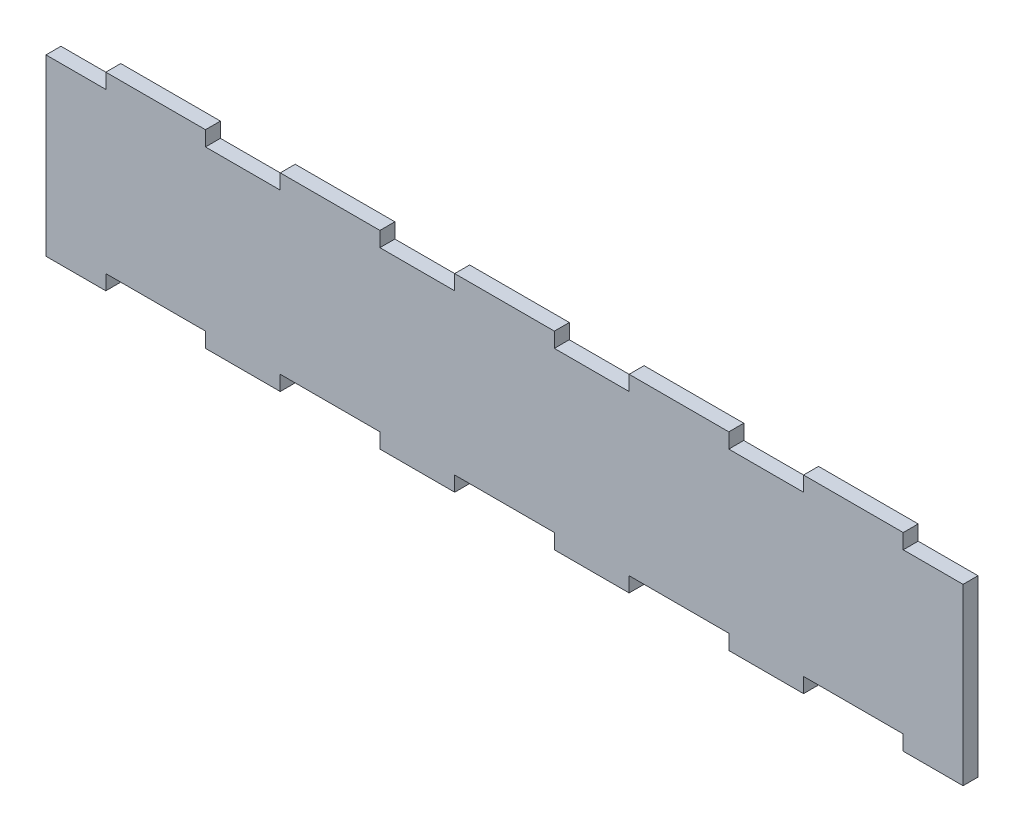
SolidWorks part; units mm, degrees
ref_plane "Front Plane" through (0, 0, 0) normal (0, 0, 1) x (1, 0, 0)
ref_plane "Top Plane" through (0, 0, 0) normal (0, 1, 0) x (1, 0, 0)
ref_plane "Right Plane" through (0, 0, 0) normal (1, 0, 0) x (0, 0, -1)
sketch "Sketch1" plane through (0, 0, 0) normal (0, 0, -1) x (1, 0, 0)
  line L0 (32, 0) -> (47, 0)
  line L1 (0, 0) -> (12, 0)
  line L2 (0, 0) -> (0, 35)
  line L3 (0, 35) -> (12, 35)
  line L4 (184, 0) -> (184, 35)
  line L5 (0, 0) -> (184, 35) construction
  line L6 (0, 35) -> (184, 0) construction
  line L7 (47, -3) -> (67, -3)
  line L8 (12, 0) -> (12, -3)
  line L9 (12, -3) -> (32, -3)
  line L10 (32, 0) -> (32, -3)
  line L11 (67, 0) -> (67, -3)
  line L12 (47, 0) -> (47, -3)
  line L13 (82, -3) -> (102, -3)
  line L14 (102, 0) -> (102, -3)
  line L15 (82, 0) -> (82, -3)
  line L16 (117, -3) -> (137, -3)
  line L17 (137, 0) -> (137, -3)
  line L18 (117, 0) -> (117, -3)
  line L19 (152, -3) -> (172, -3)
  line L20 (172, 0) -> (172, -3)
  line L21 (152, 0) -> (152, -3)
  line L22 (67, 0) -> (82, 0)
  line L23 (102, 0) -> (117, 0)
  line L24 (137, 0) -> (152, 0)
  line L25 (172, 0) -> (184, 0)
  line L26 (32, 35) -> (47, 35)
  line L27 (47, 32) -> (67, 32)
  line L28 (12, 35) -> (12, 32)
  line L29 (12, 32) -> (32, 32)
  line L30 (32, 35) -> (32, 32)
  line L31 (47, 35) -> (47, 32)
  line L32 (67, 35) -> (67, 32)
  line L33 (82, 32) -> (102, 32)
  line L34 (82, 35) -> (82, 32)
  line L35 (102, 35) -> (102, 32)
  line L36 (117, 32) -> (137, 32)
  line L37 (117, 35) -> (117, 32)
  line L38 (137, 35) -> (137, 32)
  line L39 (152, 32) -> (172, 32)
  line L40 (152, 35) -> (152, 32)
  line L41 (172, 35) -> (172, 32)
  line L42 (67, 35) -> (82, 35)
  line L43 (102, 35) -> (117, 35)
  line L44 (137, 35) -> (152, 35)
  line L45 (172, 35) -> (184, 35)
  point P4 (92, 17.5)
  point P10 (25.3866, 2.1907)
  dimension "D1" = 20
  dimension "D2" = 12
  dimension "D3" = 3
  dimension "D4" = 184
  dimension "D5" = 35
  dimension "D7" = 15
  dimension "D6" = 5
  dimension "D8" = 5
extrude "Boss-Extrude1" add sketch "Sketch1" along normal blind 3 contours L3 L28 L29 L30 L26 L31 L27 L32 L42 L34 L33 L35 L43 L37 L36 L38 L44 L40 L39 L41 L45 L4 L25 L20 L19 L21 L24 L17 L16 L18 L23 L14 L13 L15 L22 L11 L7 L12 L0 L10 L9 L8 L1 L2
